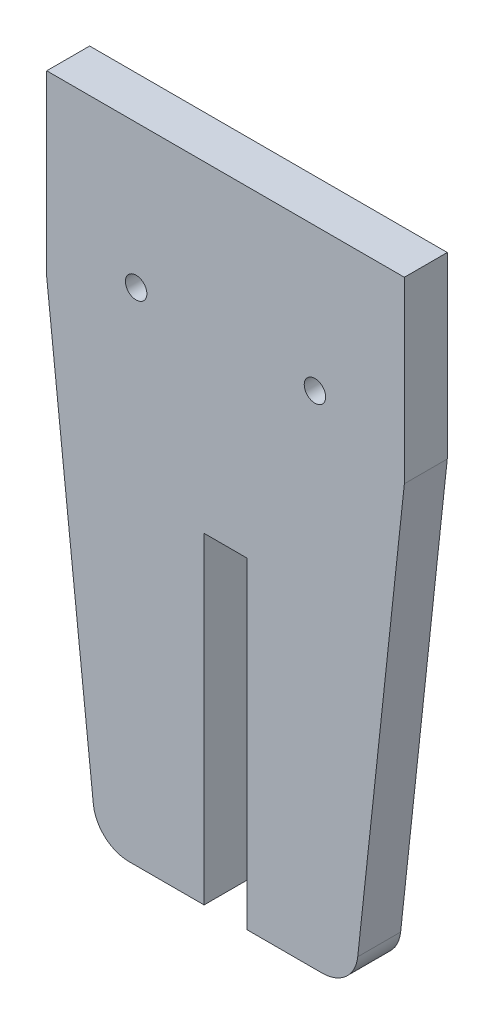
SolidWorks part; units mm, degrees
ref_plane "Front Plane" through (0, 0, 0) normal (0, 0, 1) x (1, 0, 0)
ref_plane "Top Plane" through (0, 0, 0) normal (0, 1, 0) x (1, 0, 0)
ref_plane "Right Plane" through (0, 0, 0) normal (1, 0, 0) x (0, 0, -1)
sketch "Sketch1" plane through (0, 0, 0) normal (0, 0, 1) x (1, 0, 0)
  line L1 (25, 0) -> (-25, 0)
  line L2 (18, -90) -> (-18, -90)
  line L5 (25, 0) -> (25, -25)
  line L6 (-25, 0) -> (-25, -25)
  line L7 (25, -25) -> (18, -90)
  line L8 (-25, -25) -> (-18, -90)
  point P6 (0, 0)
  point P9 (0, -90)
  dimension "D1" = 50
  dimension "D2" = 36
  dimension "D4" = 25
  dimension "D3" = 90
extrude "Boss-Extrude1" add sketch "Sketch1" along normal blind 6
sketch "Sketch3" plane through (0, 0, 6) normal (0, 0, 1) x (1, 0, 0)
  line L1 (-3, -45) -> (3, -45)
  line L2 (-3, -45) -> (-3, -90)
  line L3 (-3, -90) -> (3, -90)
  line L4 (3, -45) -> (3, -90)
  line L8 (25, 0) -> (-25, 0) construction
  point P0 (0, -45)
  dimension "D1" = 45
  dimension "D2" = 6
  dimension "D3" = 45
extrude "Cut-Extrude1" cut sketch "Sketch3" against normal through all both and the other way through all
fillet "Fillet1" radius 5 2 edges at (-18, -90, 3) (18, -90, 3)
sketch "Sketch4" plane through (0, 0, 0) normal (0, 0, -1) x (-1, 0, 0)
  line L0 (-25, 0) -> (25, 0) construction
  circle A0 centre (-12.5, -20) radius 1.5
  dimension "D1" = 3
  dimension "D2" = 20
  dimension "D3" = 12.5
extrude "Cut-Extrude2" cut sketch "Sketch4" against normal through all both and the other way through all
mirror "Mirror1" about plane through (0, 0, 0) normal (1, 0, 0) of "Cut-Extrude2"
equation "\"D1@Sketch3\"=\"D3@Sketch1\"-\"D3@Sketch3\""
